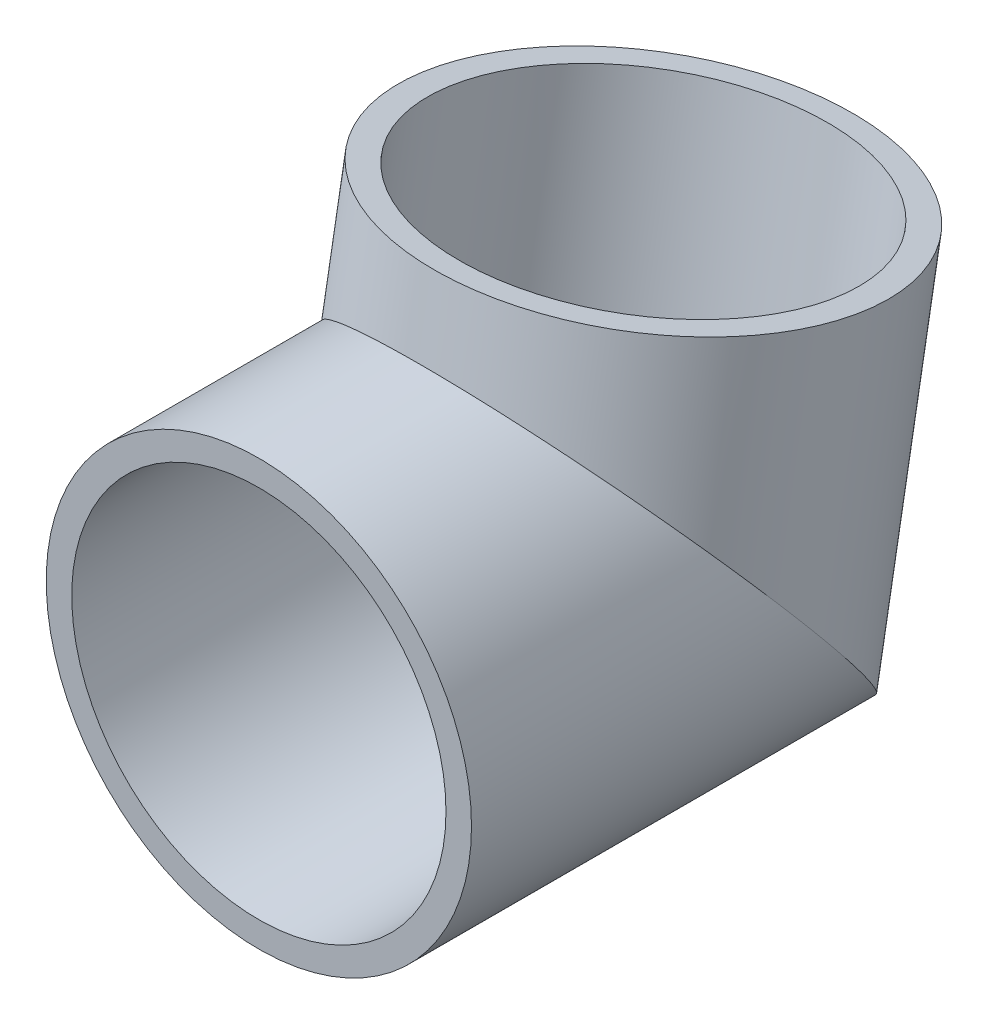
SolidWorks part; units mm, degrees
ref_plane "Front Plane" through (0, 0, 0) normal (0, 0, 1) x (1, 0, 0)
ref_plane "Top Plane" through (0, 0, 0) normal (0, 1, 0) x (1, 0, 0)
ref_plane "Right Plane" through (0, 0, 0) normal (1, 0, 0) x (0, 0, -1)
sketch "Sketch1" plane through (0, 0, 0) normal (1, 0, 0) x (0, 0, -1)
  line L0 (0, 0) -> (40, 0)
  line L1 (40, 0) -> (45.2094, 29.5442)
  line L2 (40, 0) -> (47.2364, 0) construction
  dimension "D1" = 80
sketch "Sketch3" plane through (0, 0, 0) normal (0, 0, 1) x (1, 0, 0)
  circle A0 centre (0, 0) radius 22
  circle A1 centre (0, 0) radius 25
sweep "Sweep1" add profiles "Sketch3" path "Sketch1"
